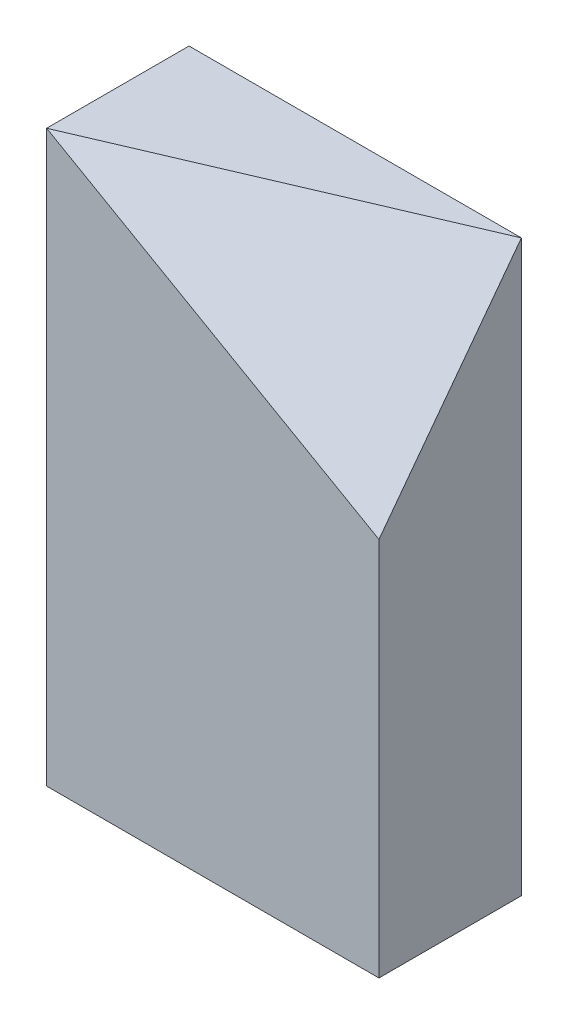
SolidWorks part; units mm, degrees
ref_plane "Front Plane" through (0, 0, 0) normal (0, 0, 1) x (1, 0, 0)
ref_plane "Top Plane" through (0, 0, 0) normal (0, 1, 0) x (1, 0, 0)
ref_plane "Right Plane" through (0, 0, 0) normal (1, 0, 0) x (0, 0, -1)
sketch "Sketch1" plane through (0, 0, 0) normal (0, 0, 1) x (1, 0, 0)
  line L0 (0, 0) -> (88.9, 0)
  line L1 (88.9, 0) -> (88.9, 152.4)
  line L2 (88.9, 152.4) -> (0, 152.4)
  line L3 (0, 152.4) -> (0, 0)
  dimension "D1" = 152.4
  dimension "D2" = 88.9
extrude "Boss-Extrude1" add sketch "Sketch1" along normal blind 38.1
sketch "Sketch2" plane through (0, 152.4, 0) normal (0, 1, 0) x (1, 0, 0)
  line L2 (0, -38.1) -> (0, 0)
  line L3 (0, 0) -> (88.9, 0)
  line L4 (88.9, 0) -> (0, -38.1)
  line L5 (0, -38.1) -> (88.9, -38.1) construction
sketch "Sketch4" plane through (0, 0, 38.1) normal (0, 0, 1) x (1, 0, 0)
  line L0 (0, 152.4) -> (88.9, 101.6)
  line L1 (88.9, 0) -> (88.9, 152.4) construction
  dimension "D1" = 50.8
ref_plane "Plane1" through (37.4042, 65.4574, 87.2766) normal (0.3243, 0.5676, 0.7568) x (0.9459, -0.1946, -0.2595)
other "SurfaceCut1"
